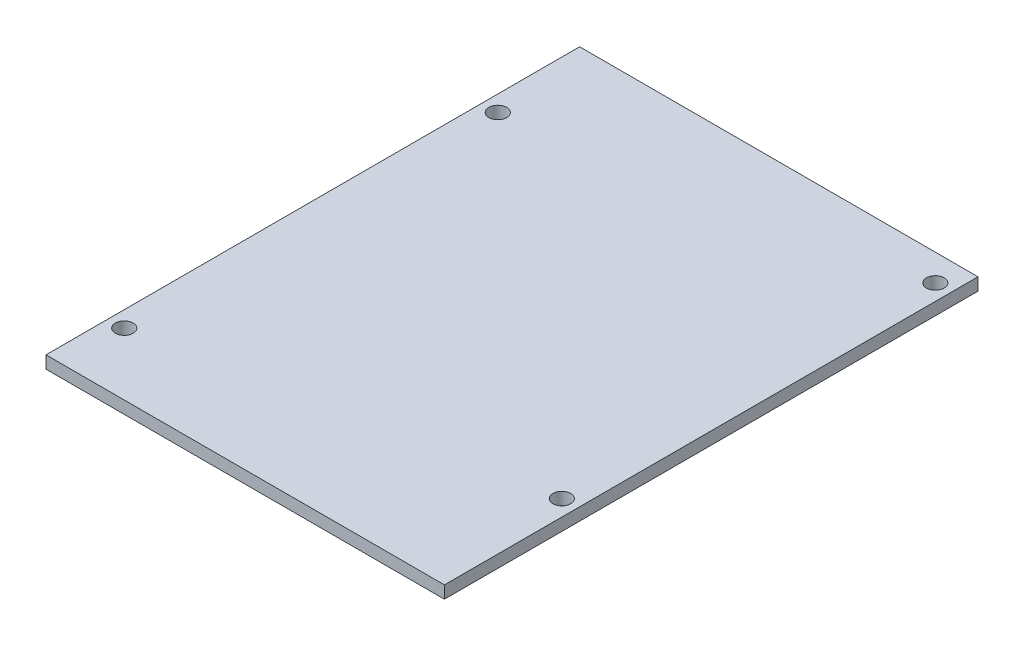
SolidWorks part; units mm, degrees
material "Balsa"
ref_plane "Plan de face" through (0, 0, 0) normal (0, 0, 1) x (1, 0, 0)
ref_plane "Plan de dessus" through (0, 0, 0) normal (0, 1, 0) x (1, 0, 0)
ref_plane "Plan de droite" through (0, 0, 0) normal (1, 0, 0) x (0, 0, -1)
sketch "Esquisse1" plane through (0, 0, 0) normal (0, 1, 0) x (1, 0, 0)
  line L0 (-56, 0) -> (56, 0) construction
  line L1 (-56, -75) -> (56, -75)
  line L2 (-56, -75) -> (-56, 75)
  line L3 (-56, 75) -> (56, 75)
  line L4 (56, -75) -> (56, 75)
  dimension "D1" = 112
  dimension "D2" = 150
extrude "Boss.-Extru.1" add sketch "Esquisse1" along normal blind 3.5
sketch "Esquisse2" plane through (0, 3.5, 0) normal (0, 1, 0) x (1, 0, 0)
  line L0 (56, 75) -> (-56, 75) construction
  line L1 (56, -75) -> (56, 75) construction
  line L2 (-56, 75) -> (-56, -75) construction
  line L3 (-56, -75) -> (56, -75) construction
  circle A0 centre (51.5, 67.5) radius 2.5
  circle A1 centre (-51.5, 47.5) radius 2.5
  circle A2 centre (51.5, -37.5) radius 2.5
  circle A4 centre (-51.5, -57.5) radius 2.5
  dimension "D1" = 5
  dimension "D4" = 5
  dimension "D7" = 5
  dimension "D12" = 5
  dimension "D2" = 7.5
  dimension "D3" = 4.5
  dimension "D5" = 4.5
  dimension "D6" = 27.5
  dimension "D8" = 4.5
  dimension "D9" = 37.5
  dimension "D10" = 17.5
  dimension "D11" = 4.5
extrude "Enlèv. mat.-Extru.1" cut sketch "Esquisse2" against normal up to next
